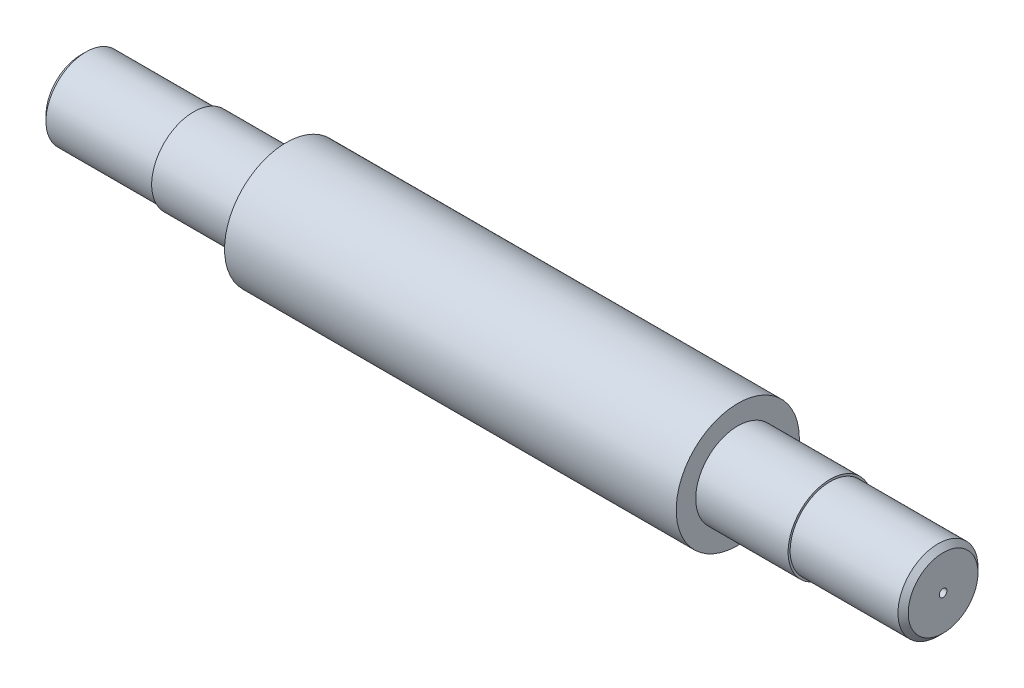
SolidWorks part; units mm, degrees
ref_plane "Front Plane" through (0, 0, 0) normal (0, 0, 1) x (1, 0, 0)
ref_plane "Top Plane" through (0, 0, 0) normal (0, 1, 0) x (1, 0, 0)
ref_plane "Right Plane" through (0, 0, 0) normal (1, 0, 0) x (0, 0, -1)
sketch "Sketch1" plane through (0, 0, 0) normal (1, 0, 0) x (0, 0, -1)
  circle A0 centre (0, 0) radius 60
  dimension "D1" = 120
extrude "Boss-Extrude1" add sketch "Sketch1" along normal mid plane 440
sketch "Sketch2" plane through (0, 0, 0) normal (1, 0, 0) x (0, 0, -1)
  circle A0 centre (0, 0) radius 41
  dimension "D1" = 82
extrude "Boss-Extrude2" add sketch "Sketch2" along normal mid plane 620
sketch "Sketch3" plane through (0, 0, 0) normal (1, 0, 0) x (0, 0, -1)
  circle A0 centre (0, 0) radius 39
  dimension "D1" = 78
extrude "Boss-Extrude3" add sketch "Sketch3" along normal mid plane 840
sketch "Sketch4" plane through (420, 0, 0) normal (1, 0, 0) x (0, 0, -1)
  circle A0 centre (0, 0) radius 3.75
  dimension "D1" = 7.5
extrude "Cut-Extrude1" cut sketch "Sketch4" against normal blind 6.25
sketch "Sketch5" plane through (-420, 0, 0) normal (-1, 0, 0) x (0, 0, 1)
  circle A0 centre (0, 0) radius 3.6
  dimension "D1" = 7.2
extrude "Cut-Extrude2" cut sketch "Sketch5" against normal blind 6.25
chamfer "Chamfer1" distance 5 angle 45 2 edges at (-420, 0, -39) (420, 0, -39)
